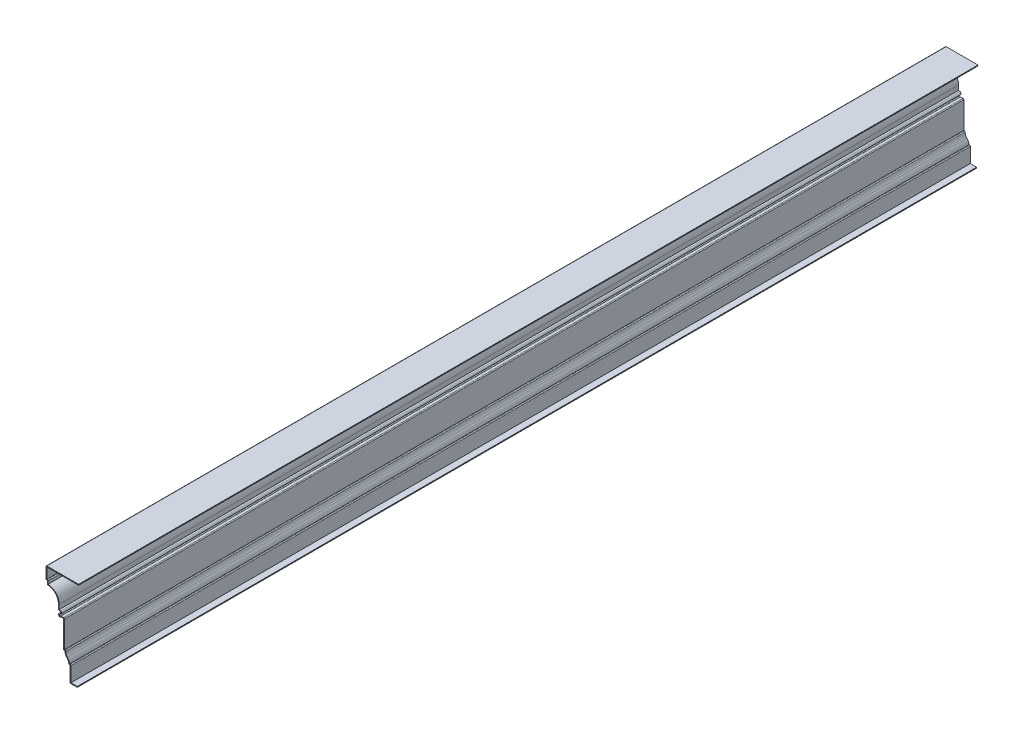
SolidWorks part; units mm, degrees
ref_plane "Front Plane" through (0, 0, 0) normal (0, 0, 1) x (1, 0, 0)
ref_plane "Top Plane" through (0, 0, 0) normal (0, 1, 0) x (1, 0, 0)
ref_plane "Right Plane" through (0, 0, 0) normal (1, 0, 0) x (0, 0, -1)
sketch "Sketch1" plane through (0, 0, 0) normal (0, 0, 1) x (1, 0, 0)
  line L0 (0, 0) -> (-8.7312, 0)
  line L1 (-8.7312, 0) -> (-8.7312, 19.05)
  line L2 (-8.7312, 19.05) -> (-10.3187, 19.05)
  line L3 (-15.0812, 30.9563) -> (-16.6687, 30.9563)
  line L4 (-16.6687, 30.9563) -> (-16.6687, 64.2938)
  line L5 (-16.6687, 64.2938) -> (-19.691, 64.2938)
  line L6 (-23.0188, 70.2469) -> (-23.0188, 76.5969)
  line L7 (-36.5125, 90.0906) -> (-36.5125, 94.4563)
  line L8 (-36.5125, 94.4563) -> (-38.1, 94.4563)
  line L9 (-38.1, 94.4563) -> (-38.1, 109.5375)
  line L10 (-38.1, 109.5375) -> (1.5875, 109.5375)
  line L11 (-22.1482, 67.1311) -> (-20.2501, 68.3515)
  line L12 (-23.0188, 70.2469) -> (-20.4635, 69.624)
  arc A0 (-10.3187, 19.05) -> (-12.7, 25.0031) centre (-18.9508, 19.05) ccw
  arc A1 (-12.7, 25.0031) -> (-15.0812, 30.9563) centre (-6.4492, 30.9562) cw
  arc A2 (-22.1482, 67.1311) -> (-19.691, 64.2938) centre (-21.1229, 65.5364) ccw
  arc A3 (-20.4635, 69.624) -> (-20.2501, 68.3515) centre (-20.6297, 68.942) cw
  arc A4 (-23.0188, 76.5969) -> (-36.5125, 90.0906) centre (-36.5125, 76.5969) ccw
  point P10 (0, 0)
  point P24 (-21.1229, 65.5364)
  point P25 (0, 0)
  point P26 (-12.798, 25.1938)
  point P27 (-12.8408, 25.579)
  dimension "D9" = 6.35
  dimension "D17" = 1.8959
  dimension "D18" = 0.702
  dimension "D1" = 1.5875
  dimension "D2" = 8.7312
  dimension "D3" = 1.5875
  dimension "D4" = 4.7625
  dimension "D5" = 1.5875
  dimension "D6" = 11.9062
  dimension "D7" = 19.05
  dimension "D8" = 33.3375
  dimension "D10" = 5.9531
  dimension "D11" = 4.3656
  dimension "D12" = 15.0812
  dimension "D13" = 39.6875
  dimension "D14" = 19.8438
  dimension "D15" = 13.4937
  dimension "D16" = 1.5875
  dimension "D19" = 2.6301
  dimension "D20" = 2.2566
  dimension "D21" = 1.3049
  dimension "D22" = 2.3813
  dimension "D23" = 5.9531
extrude "Extrude-Thin1" add sketch "Sketch1" against normal blind 1095.375 thin
fillet "Fillet1" radius 1.016 12 edges at (-8.7312, 0, -547.6875) (-7.7153, 20.066, -547.6875) (-10.3187, 19.05, -547.6875) (-13.9972, 31.9723, -547.6875) (-16.6687, 30.9563, -547.6875) (-15.6527, 65.3097, -547.6875) (-20.2727, 65.3097, -547.6875) (-23.0188, 70.2469, -547.6875) (-36.5125, 90.0906, -547.6875) (-35.4965, 95.4723, -547.6875) (-38.1, 94.4563, -547.6875) (-38.1, 109.5375, -547.6875)
